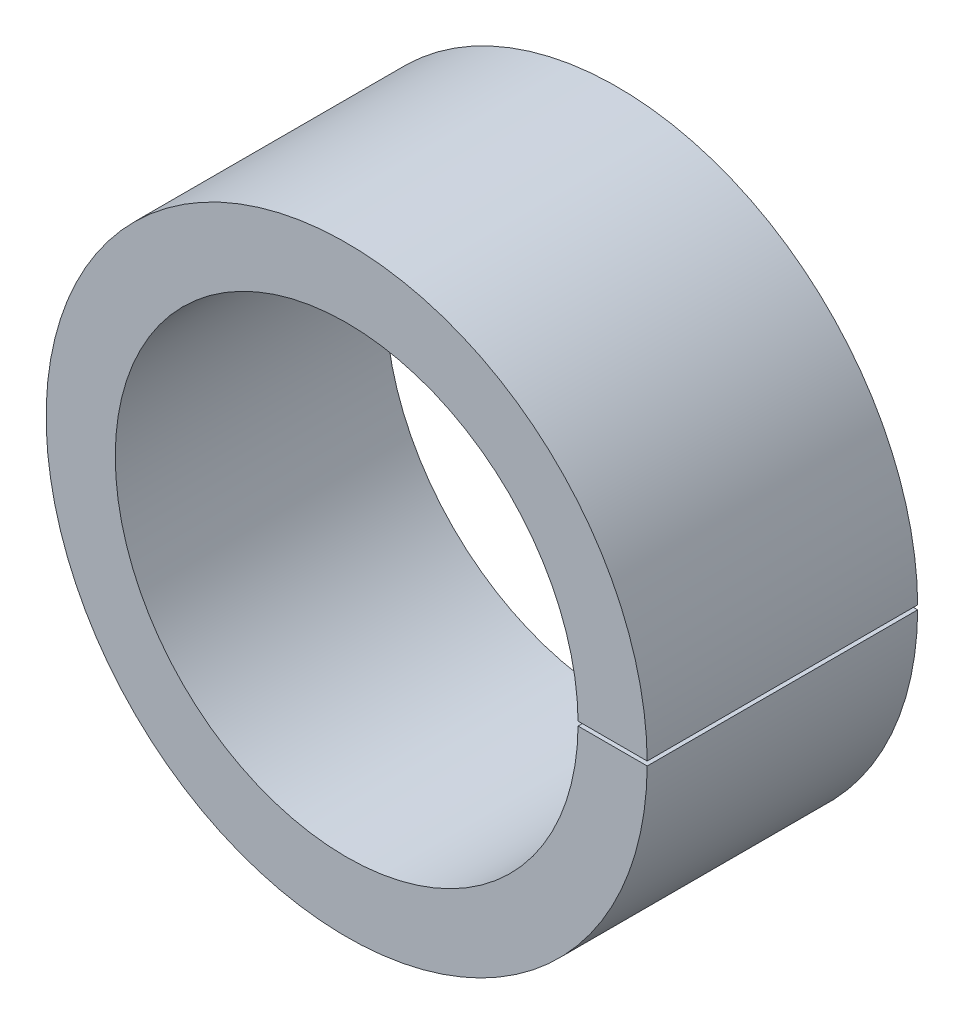
SolidWorks part; units mm, degrees
ref_plane "Front Plane" through (0, 0, 0) normal (0, 0, 1) x (1, 0, 0)
ref_plane "Top Plane" through (0, 0, 0) normal (0, 1, 0) x (1, 0, 0)
ref_plane "Right Plane" through (0, 0, 0) normal (1, 0, 0) x (0, 0, -1)
sketch "Sketch1" plane through (0, 0, 0) normal (0, 0, 1) x (1, 0, 0)
  line L0 (-6.35, 0) -> (6.35, 0) construction
  line L1 (0, 0) -> (3.4574, -3.4574) construction
  line L2 (4.8895, 0) -> (-4.8895, 0) construction
  circle A0 centre (0, 0) radius 6.35 construction
  circle A1 centre (0, 0) radius 4.8895 construction
  point P4 (0, 6.35)
  point P7 (0, 0)
  point P8 (0, 4.8895)
  point P9 (0, -4.8895)
  point P12 (3.4574, -3.4574)
  point P14 (0, 0)
  dimension "D1" = 45
  dimension "OD" = 12.7
  dimension "ID" = 9.779
sketch "Sketch2" plane through (0, 0, 0) normal (1, 0, 0) x (0, 0, -1)
  line L0 (-4.7625, 6.35) -> (4.7625, 6.35) construction
  line L1 (-4.7625, 4.8895) -> (4.7625, 4.8895) construction
  line L3 (4.7625, -4.8895) -> (-4.7625, -4.8895) construction
  point P2 (0, 6.35)
  point P6 (0, 4.8895)
  point P9 (0, -4.8895)
  dimension "Length" = 9.525
sketch "Sketch3" plane through (0, 0, 0) normal (0, 0, 1) x (1, 0, 0)
  line L0 (0, -0.045) -> (0, 0.045) construction
  line L1 (0, 0.045) -> (6.3498, 0.045) construction
  line L2 (0, -0.045) -> (6.3498, -0.045) construction
  line L3 (4.8893, 0.045) -> (6.3498, 0.045)
  line L4 (4.8893, -0.045) -> (6.3498, -0.045)
  circle A1 centre (0, 0) radius 6.35 construction
  circle A4 centre (0, 0) radius 4.8895 construction
  arc A5 (6.3498, 0.045) -> (6.3498, -0.045) centre (0, 0) ccw
  arc A6 (4.8893, 0.045) -> (4.8893, -0.045) centre (0, 0) ccw
  point P7 (0, 0)
  dimension "D1" = 0.09
extrude "Boss-Extrude1" add sketch "Sketch3" along normal up to vertex (4.7625 mm away) and the other way up to vertex (4.7625 mm away) up to point (0, 6.35, 4.7625) other way up to point (0, 6.35, -4.7625)
sketch "Sketch4" plane through (0, 0, -4.7625) normal (0, 0, -1) x (-1, 0, 0)
  line L1 (-12.7307, 11.379) -> (11.3134, 11.379)
  line L2 (-12.7307, 11.379) -> (-12.7307, -11.1427)
  line L3 (-12.7307, -11.1427) -> (11.3134, -11.1427)
  line L4 (11.3134, 11.379) -> (11.3134, -11.1427)
extrude "Cut-Extrude1" cut sketch "Sketch4" against normal blind 3.81
